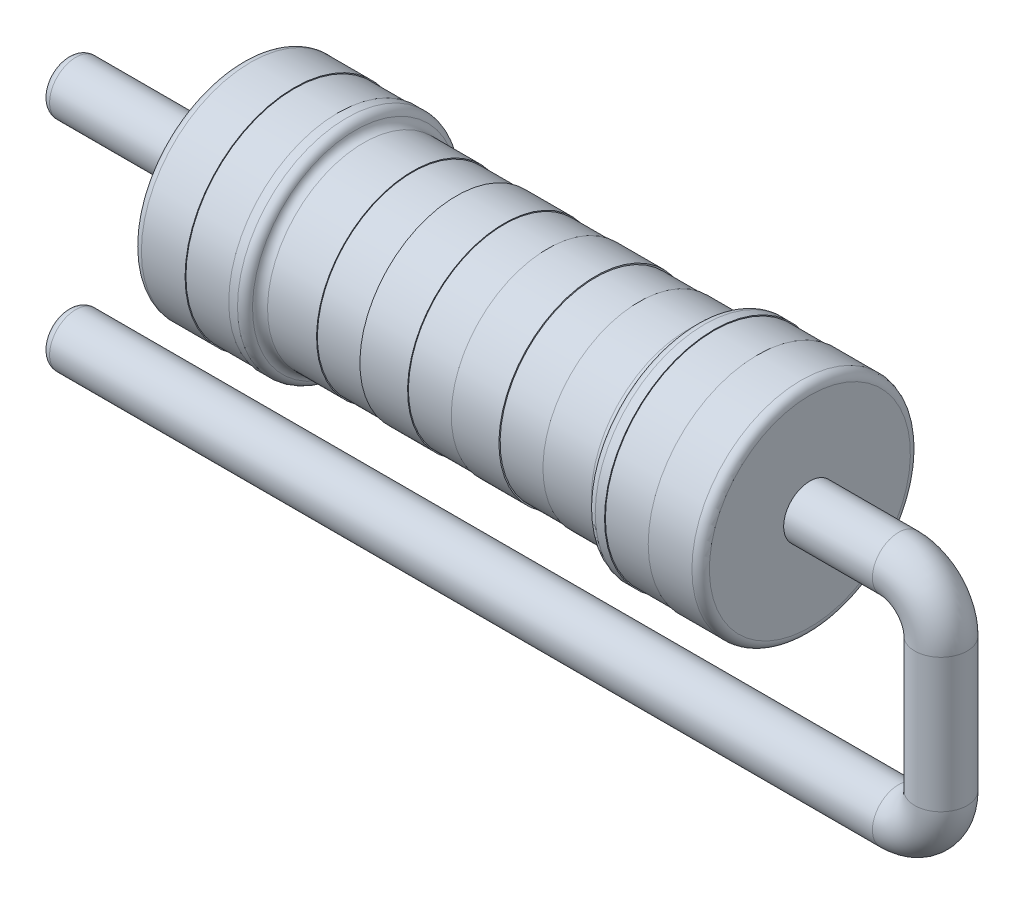
SolidWorks part; units mm, degrees
ref_plane "Front Plane" through (0, 0, 0) normal (0, 0, 1) x (1, 0, 0)
ref_plane "Top Plane" through (0, 0, 0) normal (0, 1, 0) x (1, 0, 0)
ref_plane "Right Plane" through (0, 0, 0) normal (1, 0, 0) x (0, 0, -1)
sketch "Sketch1" plane through (0, 0, 0) normal (0, 0, 1) x (1, 0, 0)
  line L0 (-3.25, 0) -> (3.25, 0)
  line L1 (3.25, 0) -> (3.25, -1.25)
  line L2 (3.25, -1.25) -> (2.65, -1.25)
  line L3 (2.65, -1.25) -> (2.65, -1.24)
  line L4 (2.65, -1.24) -> (2.15, -1.24)
  line L5 (2.15, -1.24) -> (2.15, -1.25)
  line L6 (2.15, -1.25) -> (1.95, -1.25)
  line L7 (1.95, -1.25) -> (1.95, -1.1)
  line L8 (1.95, -1.1) -> (1.2955, -1.1)
  line L9 (1.2955, -1.1) -> (1.2955, -1.09)
  line L10 (1.2955, -1.09) -> (0.7955, -1.09)
  line L11 (0.7955, -1.09) -> (0.7955, -1.1038)
  line L12 (0.7955, -1.1038) -> (0.25, -1.1038)
  line L13 (0.25, -1.1038) -> (0.25, -1.0938)
  line L14 (0.25, -1.0938) -> (-0.25, -1.0938)
  line L16 (-0.25, -1.1038) -> (-0.25, -1.0938)
  line L17 (-0.7955, -1.1038) -> (-0.25, -1.1038)
  line L18 (-0.7955, -1.09) -> (-0.7955, -1.1038)
  line L19 (-1.2955, -1.09) -> (-0.7955, -1.09)
  line L20 (-1.2955, -1.1) -> (-1.2955, -1.09)
  line L21 (-1.95, -1.1) -> (-1.2955, -1.1)
  line L22 (-1.95, -1.25) -> (-1.95, -1.1)
  line L23 (-2.15, -1.25) -> (-1.95, -1.25)
  line L24 (-2.15, -1.24) -> (-2.15, -1.25)
  line L25 (-2.65, -1.24) -> (-2.15, -1.24)
  line L26 (-2.65, -1.25) -> (-2.65, -1.24)
  line L27 (-3.25, -1.25) -> (-2.65, -1.25)
  line L28 (-3.25, 0) -> (-3.25, -1.25)
  point P16 (0, 0)
  dimension "D2" = 1.25
  dimension "D3" = 1.3
  dimension "D4" = 0.5
  dimension "D5" = 0.6
  dimension "D6" = 0.01
  dimension "D7" = 0.01
  dimension "D8" = 0.15
  dimension "D9" = 0.01
  dimension "D10" = 0.0138
  dimension "D11" = 0.01
  dimension "D12" = 0.5
revolve "Revolve3" add sketch "Sketch1" angle 360 about L0
fillet "Fillet3" radius 0.1 2 edges at (-3.25, -1.25, 0) (1.95, -1.1, 0)
fillet "Fillet4" radius 0.1 2 edges at (1.95, -1.25, 0) (-1.95, -1.25, 0)
fillet "Fillet5" radius 0.1 2 edges at (-1.95, -1.1, 0) (3.25, -1.25, 0)
sketch "Sketch3" plane through (3.25, 0, 0) normal (1, 0, 0) x (0, 0, -1)
  circle A0 centre (0, 0) radius 0.3
sketch3d "3DSketch2"
  line L0 (3.25, 0, 0) -> (4.2656, 0, 0)
  line L1 (4.75, -0.4844, 0) -> (4.75, -2.0156, 0)
  line L2 (4.2656, -2.5, 0) -> (-5.25, -2.5, 0)
  arc A0 (4.2656, -2.5, 0) -> (4.75, -2.0156, 0) centre (4.2656, -2.0156, 0) ccw
  arc A1 (4.75, -0.4844, 0) -> (4.2656, 0, 0) centre (4.2656, -0.4844, 0) ccw
  point P7 (4.75, -2.5, 0)
  point P8 (4.2656, -2.0156, 0.4844)
  point P11 (4.75, 0, 0)
  point P12 (4.2656, -0.4844, 0.4844)
  dimension "D4" = 0.4844
  dimension "D1" = 1.5
  dimension "D2" = 2.5
  dimension "D3" = 10
sketch "Sketch4" plane through (-3.25, 0, 0) normal (-1, 0, 0) x (0, 0, 1)
  circle A0 centre (0, 0) radius 0.3
  point P3 (0, 0)
sketch3d "3DSketch3"
  line L0 (-3.25, 0, 0) -> (-5.25, 0, 0)
  dimension "D1" = 2
sweep "Sweep2" add profiles "Sketch3" path "3DSketch2"
sweep "Sweep3" add profiles "Sketch4" path "3DSketch3"
fillet "Fillet7" radius 0.1 2 edges at (-5.25, -2.8, 0) (-5.25, -0.3, 0)
